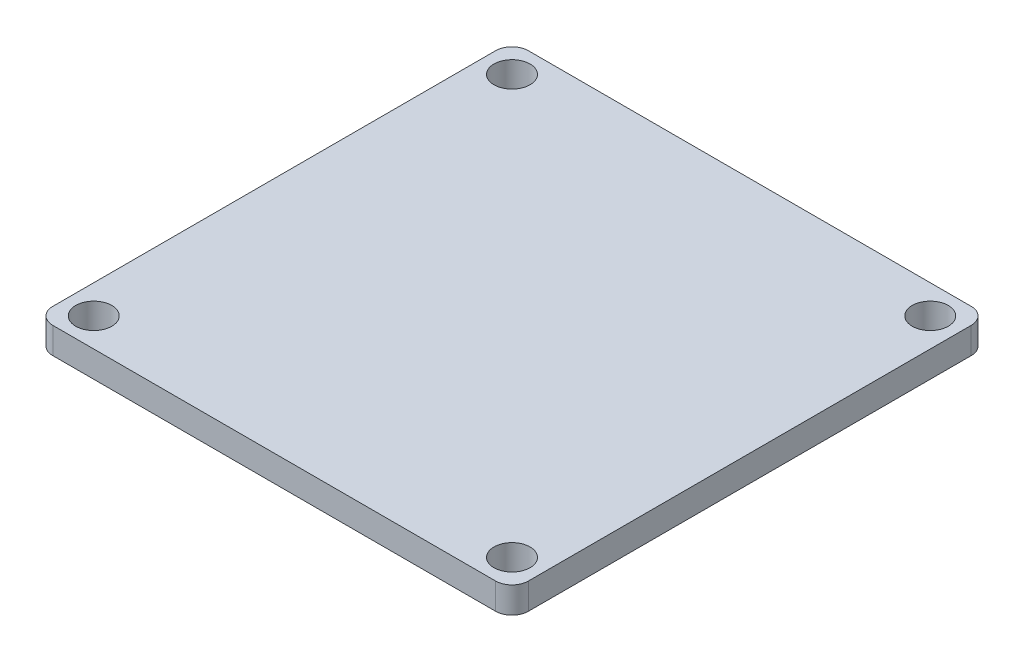
SolidWorks part; units mm, degrees
ref_plane "Ebene vorne" through (0, 0, 0) normal (0, 0, 1) x (1, 0, 0)
ref_plane "Ebene oben" through (0, 0, 0) normal (0, 1, 0) x (1, 0, 0)
ref_plane "Ebene rechts" through (0, 0, 0) normal (1, 0, 0) x (0, 0, -1)
sketch "Skizze1" plane through (0, 0, 0) normal (0, 1, 0) x (1, 0, 0)
  line L1 (-14.5, -14.5) -> (14.5, -14.5)
  line L2 (-14.5, -14.5) -> (-14.5, 14.5)
  line L3 (-14.5, 14.5) -> (14.5, 14.5)
  line L4 (14.5, -14.5) -> (14.5, 14.5)
  line L5 (-14.5, -14.5) -> (14.5, 14.5) construction
  line L6 (-14.5, 14.5) -> (14.5, -14.5) construction
  line L7 (-12.75, -12.75) -> (12.75, -12.75) construction
  line L8 (-12.75, -12.75) -> (-12.75, 12.75) construction
  line L9 (-12.75, 12.75) -> (12.75, 12.75) construction
  line L10 (12.75, -12.75) -> (12.75, 12.75) construction
  line L11 (-12.75, -12.75) -> (12.75, 12.75) construction
  line L12 (-12.75, 12.75) -> (12.75, -12.75) construction
  circle A0 centre (-12.75, 12.75) radius 1.1
  circle A1 centre (12.75, 12.75) radius 1.1
  circle A2 centre (12.75, -12.75) radius 1.1
  circle A3 centre (-12.75, -12.75) radius 1.1
  point P0 (0, 0)
  point P6 (0, 0)
  dimension "D3" = 2.2
  dimension "D1" = 29
  dimension "D2" = 25.5
extrude "Aufsatz-Linear austragen1" add sketch "Skizze1" along normal blind 1.6
fillet "Verrundung1" radius 1 4 edges at (-14.5, 0.8, -14.5) (14.5, 0.8, -14.5) (14.5, 0.8, 14.5) (-14.5, 0.8, 14.5)
